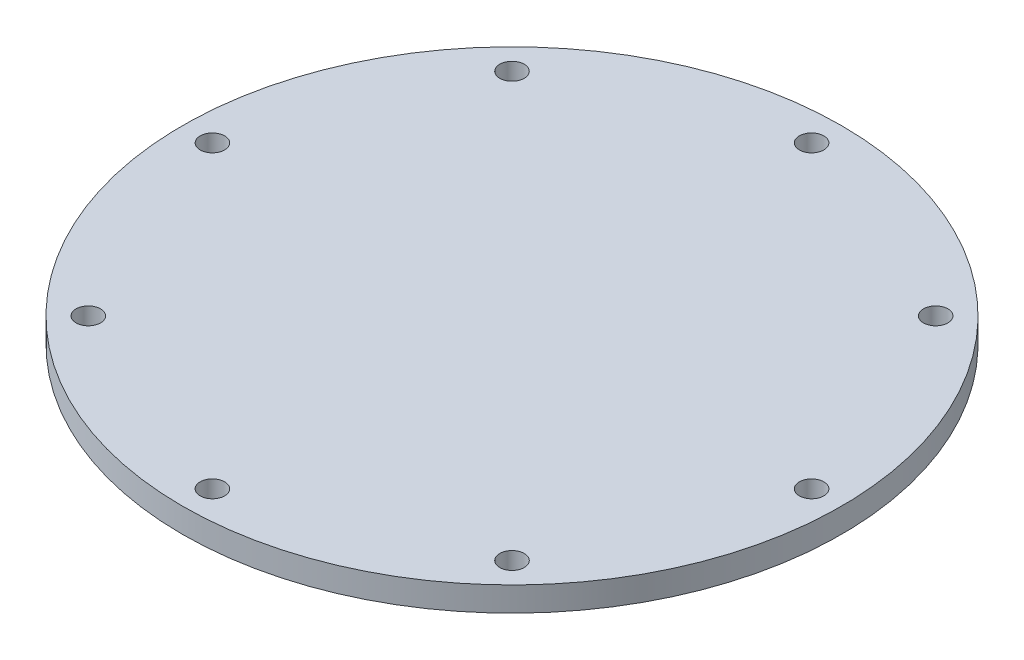
SolidWorks part; units mm, degrees
material "ABS PC"
ref_plane "Front Plane" through (0, 0, 0) normal (0, 0, 1) x (1, 0, 0)
ref_plane "Top Plane" through (0, 0, 0) normal (0, 1, 0) x (1, 0, 0)
ref_plane "Right Plane" through (0, 0, 0) normal (1, 0, 0) x (0, 0, -1)
sketch "Sketch1" plane through (0, 0, 0) normal (0, 1, 0) x (1, 0, 0)
  circle A18 centre (0, 0) radius 26.95
  circle A20 centre (0, 24.5) radius 1
  circle A21 centre (17.3241, 17.3241) radius 1
  circle A22 centre (24.5, 0) radius 1
  circle A23 centre (17.3241, -17.3241) radius 1
  circle A24 centre (0, -24.5) radius 1
  circle A25 centre (-17.3241, -17.3241) radius 1
  circle A26 centre (-24.5, 0) radius 1
  circle A27 centre (-17.3241, 17.3241) radius 1
  point P20 (0, 0)
  dimension "D3" = 24.5
  dimension "D4" = 8
  dimension "D1" = 53.9
  dimension "D2" = 2
extrude "Boss-Extrude1" add sketch "Sketch1" along normal blind 2
